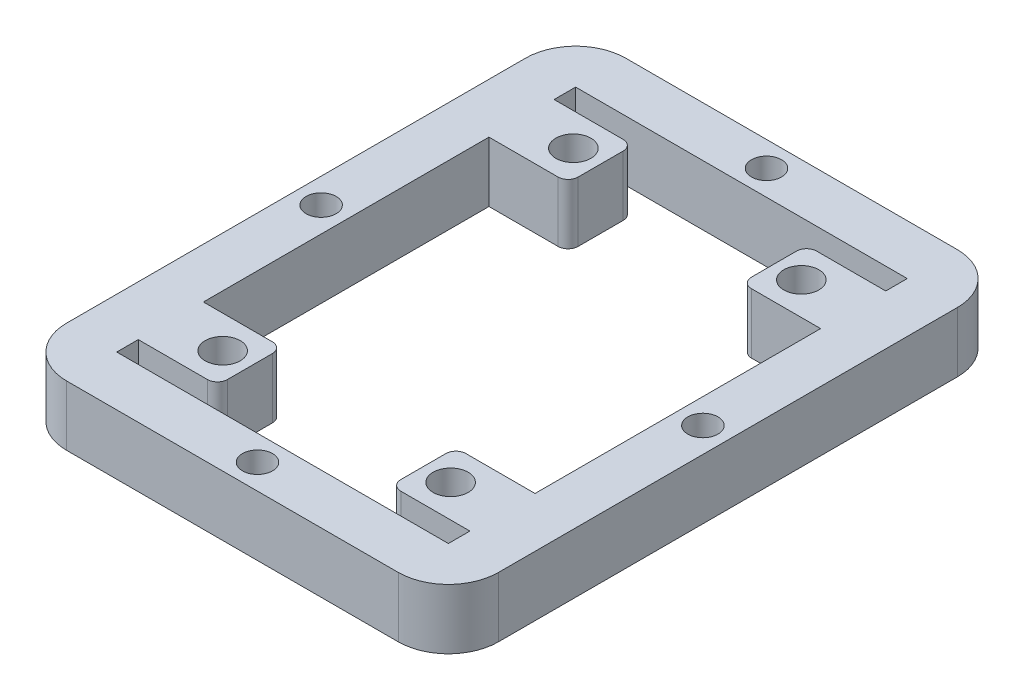
SolidWorks part; units mm, degrees
ref_plane "Front Plane" through (0, 0, 0) normal (0, 0, 1) x (1, 0, 0)
ref_plane "Top Plane" through (0, 0, 0) normal (0, 1, 0) x (1, 0, 0)
ref_plane "Right Plane" through (0, 0, 0) normal (1, 0, 0) x (0, 0, -1)
sketch "Sketch1" plane through (0, 0, 0) normal (0, 1, 0) x (1, 0, 0)
  line L0 (-14.25, 0) -> (14.25, 0) construction
  line L1 (-14.25, -20.75) -> (14.25, -20.75) construction
  line L2 (-14.25, -20.75) -> (-14.25, 14.25) construction
  line L3 (-14.25, 20.75) -> (14.25, 20.75) construction
  line L4 (14.25, -20.75) -> (14.25, 14.25) construction
  line L5 (-14.25, -20.75) -> (14.25, 20.75) construction
  line L6 (-14.25, 20.75) -> (14.25, -20.75) construction
  line L7 (0, 20.75) -> (0, -20.75) construction
  line L8 (14.25, -14.25) -> (8.65, -14.25)
  line L9 (14.25, 20.75) -> (8.65, 20.75)
  line L10 (0, 0) -> (0, 25.4) construction
  line L11 (14.25, 14.25) -> (8.65, 14.25)
  line L12 (8.65, 20.75) -> (8.65, 14.25)
  line L13 (8.65, -20.75) -> (8.65, -14.25)
  line L14 (14.25, -20.75) -> (8.65, -20.75)
  line L15 (-14.25, -20.75) -> (-8.65, -20.75)
  line L16 (-8.65, -20.75) -> (-8.65, -14.25)
  line L17 (-14.25, -14.25) -> (-8.65, -14.25)
  line L18 (-14.25, 14.25) -> (-8.65, 14.25)
  line L19 (-8.65, 20.75) -> (-8.65, 14.25)
  line L20 (-14.25, 20.75) -> (-8.65, 20.75)
  line L21 (16.55, -22.9) -> (16.55, -20.75)
  line L22 (16.55, -22.9) -> (-16.55, -22.9)
  line L23 (16.55, 22.9) -> (-16.55, 22.9)
  line L24 (-16.55, -22.9) -> (-16.55, -20.75)
  line L25 (16.55, -22.9) -> (-16.55, 22.9) construction
  line L26 (16.55, 22.9) -> (-16.55, -22.9) construction
  line L27 (21.55, -27.9) -> (21.55, 27.9)
  line L28 (21.55, -27.9) -> (-21.55, -27.9)
  line L29 (21.55, 27.9) -> (-21.55, 27.9)
  line L30 (-21.55, -27.9) -> (-21.55, 27.9)
  line L31 (21.55, -27.9) -> (-21.55, 27.9) construction
  line L32 (21.55, 27.9) -> (-21.55, -27.9) construction
  line L33 (14.25, 20.75) -> (16.55, 20.75)
  line L34 (14.25, 14.25) -> (16.55, 14.25)
  line L35 (14.25, -14.25) -> (16.55, -14.25)
  line L36 (14.25, -20.75) -> (16.55, -20.75)
  line L37 (-14.25, -14.25) -> (-16.55, -14.25)
  line L38 (-14.25, -20.75) -> (-16.55, -20.75)
  line L39 (-14.25, 20.75) -> (-16.55, 20.75)
  line L40 (-16.55, 14.25) -> (-14.25, 14.25)
  line L41 (-14.25, 18.8241) -> (-14.25, 20.75) construction
  line L42 (-16.55, 20.75) -> (-16.55, 22.9)
  line L43 (-16.55, -14.25) -> (-16.55, 14.25)
  line L44 (16.55, -14.25) -> (16.55, 14.25)
  line L45 (0, -21.75) -> (0, -26.75) construction
  line L46 (16.55, 20.75) -> (16.55, 22.9)
  circle A0 centre (11.375, 17.5) radius 1.75
  circle A1 centre (11.375, -17.5) radius 1.75
  circle A2 centre (-11.375, -17.5) radius 1.75
  circle A3 centre (-11.375, 17.5) radius 1.75
  circle A4 centre (0, 25.4) radius 1.5
  circle A5 centre (-19.05, 0) radius 1.5
  circle A6 centre (19.05, 0) radius 1.5
  circle A7 centre (0, -25.4) radius 1.5
  point P0 (0, 0)
  point P30 (0, 0)
  point P35 (0, 0)
  point P37 (-21.55, 0)
  point P38 (-16.55, 0)
  point P39 (0, 22.9)
  point P40 (0, 27.9)
  dimension "D4" = 3.5
  dimension "D13" = 2.5
  dimension "D9" = 3
  dimension "D10" = 3
  dimension "D1" = 41.5
  dimension "D2" = 28.5
  dimension "D3" = 11.375
  dimension "D5" = 17.5
  dimension "D6" = 6.5
  dimension "D7" = 5.6
  dimension "D8" = 25.4
  dimension "D11" = 19.05
  dimension "D12" = 2.5
  dimension "D14" = 2.5
  dimension "D15" = 2.5
extrude "Boss-Extrude1" add sketch "Sketch1" along normal blind 6
fillet "Fillet3" radius 5 4 edges at (21.55, 3, 27.9) (-21.55, 3, 27.9) (21.55, 3, -27.9) (-21.55, 3, -27.9)
fillet "Fillet4" radius 1 8 edges at (8.65, 3, 20.75) (8.65, 3, 14.25) (-8.65, 3, 20.75) (-8.65, 3, 14.25) (8.65, 3, -20.75) (8.65, 3, -14.25) (-8.65, 3, -20.75) (-8.65, 3, -14.25)
